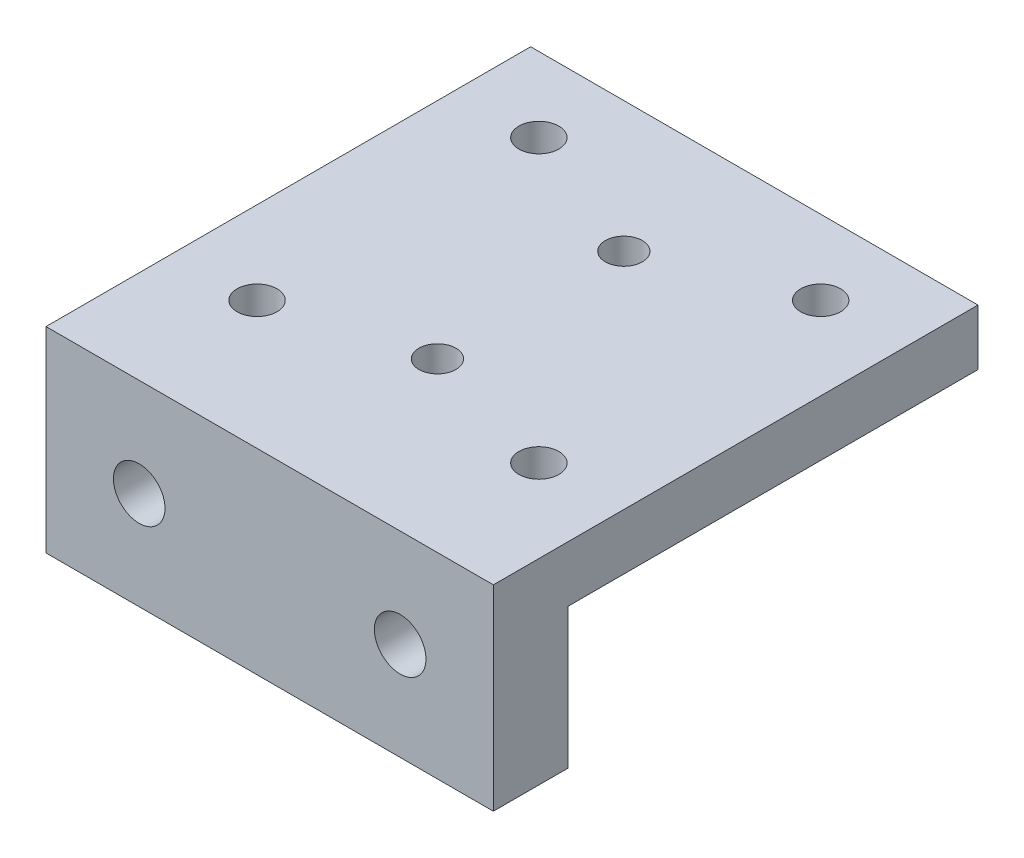
SolidWorks part; units mm, degrees
material "Copper"
ref_plane "Front Plane" through (0, 0, 0) normal (0, 0, 1) x (1, 0, 0)
ref_plane "Top Plane" through (0, 0, 0) normal (0, 1, 0) x (1, 0, 0)
ref_plane "Right Plane" through (0, 0, 0) normal (1, 0, 0) x (0, 0, -1)
sketch "Sketch1" plane through (0, 0, 0) normal (1, 0, 0) x (0, 0, -1)
  line L0 (20.6375, 0) -> (-20.6375, 0)
  line L1 (-20.6375, 0) -> (-20.6375, -16.7005)
  line L2 (-20.6375, -16.7005) -> (-14.2875, -16.7005)
  line L3 (-14.2875, -16.7005) -> (-14.2875, -4.7625)
  line L4 (-14.2875, -4.7625) -> (20.6375, -4.7625)
  line L5 (20.6375, -4.7625) -> (20.6375, 0)
  dimension "D1" = 41.275
  dimension "D2" = 16.7005
  dimension "D3" = 4.7625
  dimension "D4" = 6.35
extrude "Boss-Extrude1" add sketch "Sketch1" along normal mid plane 38.1
hole_wizard "M3 Clearance Hole1" positions "Sketch2" profile "Sketch3" hole size "M3" standard "ANSI Metric" end condition through all
sketch "Sketch2" plane through (0, -4.7625, 0) normal (0, -1, 0) x (-1, 0, 0)
  line L0 (0, 0) -> (0, 20.6375) construction
  line L1 (-19.05, 20.6375) -> (19.05, 20.6375) construction
  line L3 (0, 0) -> (-19.05, 0) construction
  line L4 (-19.05, -14.2875) -> (-19.05, 20.6375) construction
  point P0 (-12, 14.2875)
  point P20 (12, 14.2875)
  point P21 (12, -9.7125)
  point P22 (-12, -9.7125)
  dimension "D1" = 6.35
  dimension "D2" = 12
  dimension "D3" = 2
  dimension "D4" = 2
sketch "Sketch3" plane through (12, -4.7625, -14.2875) normal (1, 0, 0) x (0, 0, -1)
  line L0 (0, 0) -> (0, 4.7625)
  line L1 (0, 4.7625) -> (1.7, 4.7625)
  line L2 (1.7, 4.7625) -> (1.7, 0)
  line L5 (1.7, 0) -> (0, 0)
  line L11 (0, -6.35) -> (0, 107.95) construction
  dimension "Thru Hole Dia." = 3.4
  dimension "Thru Hole Depth" = 4.7625
hole_wizard "Tapped Hole for M3x0.5 Helicoil1" positions "Sketch4" profile "Sketch5" tap size "M3x0.5" standard "Helicoil® Metric" end condition through all
sketch "Sketch4" plane through (0, -4.7625, 0) normal (0, -1, 0) x (-1, 0, 0)
  line L0 (0, 20.6375) -> (0, -14.2875) construction
  line L1 (-19.05, 20.6375) -> (19.05, 20.6375) construction
  line L2 (-19.05, -14.2875) -> (19.05, -14.2875) construction
  point P0 (0, -6.35)
  point P2 (0, 9.525)
  dimension "D1" = 11.1125
  dimension "D2" = 15.875
sketch "Sketch5" plane through (0, -4.7625, 6.35) normal (1, 0, 0) x (0, 0, -1)
  line L0 (0, 0) -> (0, 4.7625)
  line L1 (0, 4.7625) -> (1.575, 4.7625)
  line L2 (1.575, 4.7625) -> (1.575, 0)
  line L5 (1.575, 0) -> (0, 0)
  line L11 (0, -6.35) -> (0, 107.95) construction
  dimension "Thru Tap Drill Dia." = 3.15
  dimension "Thru Tap Drill Depth" = 4.7625
cosmetic thread "Hole Thread5"
cosmetic thread "Hole Thread6"
hole_wizard "Tapped Hole for #8-32 Helicoil1" positions "Sketch7" profile "Sketch6" tap size "#8-32" standard "Helicoil® Inch" end condition through all
sketch "Sketch7" plane through (0, 0, 20.6375) normal (0, 0, 1) x (1, 0, 0)
  line L0 (19.05, 0) -> (-19.05, 0) construction
  line L1 (0, 0) -> (0, -16.7005) construction
  line L2 (19.05, -16.7005) -> (-19.05, -16.7005) construction
  line L3 (19.05, -8.3503) -> (-19.05, -8.3503) construction
  line L4 (19.05, 0) -> (19.05, -16.7005) construction
  line L5 (-19.05, 0) -> (-19.05, -16.7005) construction
  point P0 (-11.1125, -8.3503)
  point P1 (11.1125, -8.3503)
  dimension "D2" = 11.1125
  dimension "D3" = 11.1125
sketch "Sketch6" plane through (-11.1125, -8.3503, 20.6375) normal (1, 0, 0) x (0, -1, 0)
  line L0 (0, 0) -> (0, 41.275)
  line L1 (0, 41.275) -> (2.1971, 41.275)
  line L2 (2.1971, 41.275) -> (2.1971, 0)
  line L5 (2.1971, 0) -> (0, 0)
  line L11 (0, -6.35) -> (0, 107.95) construction
  dimension "Thru Tap Drill Dia." = 4.3942
  dimension "Thru Tap Drill Depth" = 41.275
cosmetic thread "Hole Thread3"
cosmetic thread "Hole Thread4"
